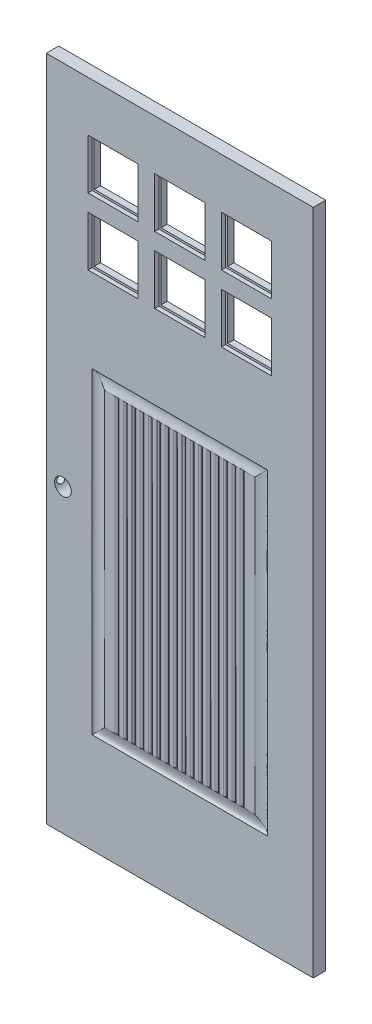
SolidWorks part; units mm, degrees
material "E-Glass Fiber"
ref_plane "Front Plane" through (0, 0, 0) normal (0, 0, 1) x (1, 0, 0)
ref_plane "Top Plane" through (0, 0, 0) normal (0, 1, 0) x (1, 0, 0)
ref_plane "Right Plane" through (0, 0, 0) normal (1, 0, 0) x (0, 0, -1)
sketch "Sketch1" plane through (0, 0, 0) normal (0, 0, 1) x (1, 0, 0)
  line L1 (-406.4, -1016) -> (406.4, -1016)
  line L2 (-406.4, -1016) -> (-406.4, 1016)
  line L3 (-406.4, 1016) -> (406.4, 1016)
  line L4 (406.4, -1016) -> (406.4, 1016)
  line L5 (-406.4, -1016) -> (406.4, 1016) construction
  line L6 (-406.4, 1016) -> (406.4, -1016) construction
  point P0 (0, 0)
  dimension "D1" = 2032
  dimension "D2" = 812.8
extrude "Boss-Extrude1" add sketch "Sketch1" along normal blind 38.1
sketch "Sketch2" plane through (0, 0, 38.1) normal (0, 0, 1) x (1, 0, 0)
  line L0 (406.4, 1016) -> (-406.4, 1016) construction
  line L1 (-279.4, 863.6) -> (-127, 863.6)
  line L2 (-279.4, 863.6) -> (-279.4, 711.2)
  line L3 (-279.4, 711.2) -> (-127, 711.2)
  line L4 (-127, 863.6) -> (-127, 711.2)
  line L5 (-279.4, 863.6) -> (-127, 711.2) construction
  line L6 (-279.4, 711.2) -> (-127, 863.6) construction
  line L7 (-406.4, 1016) -> (-406.4, -1016) construction
  line L8 (-76.2, 863.6) -> (-76.2, 711.2)
  line L9 (-76.2, 863.6) -> (76.2, 863.6)
  line L10 (76.2, 863.6) -> (76.2, 711.2)
  line L11 (-76.2, 711.2) -> (76.2, 711.2)
  line L12 (127, 863.6) -> (127, 711.2)
  line L13 (127, 863.6) -> (279.4, 863.6)
  line L14 (279.4, 863.6) -> (279.4, 711.2)
  line L15 (127, 711.2) -> (279.4, 711.2)
  line L16 (-76.2, 660.4) -> (-76.2, 508)
  line L17 (-76.2, 660.4) -> (76.2, 660.4)
  line L18 (76.2, 660.4) -> (76.2, 508)
  line L19 (-76.2, 508) -> (76.2, 508)
  line L20 (127, 660.4) -> (127, 508)
  line L21 (127, 660.4) -> (279.4, 660.4)
  line L22 (279.4, 660.4) -> (279.4, 508)
  line L23 (127, 508) -> (279.4, 508)
  line L24 (-279.4, 660.4) -> (-279.4, 508)
  line L25 (-279.4, 660.4) -> (-127, 660.4)
  line L26 (-127, 660.4) -> (-127, 508)
  line L27 (-279.4, 508) -> (-127, 508)
  line L30 (-406.4, -1016) -> (406.4, -1016) construction
  circle A0 centre (-355.6, -101.6) radius 25.4
  point P0 (-203.2, 787.4)
  dimension "D9" = 50.8
  dimension "D1" = 152.4
  dimension "D2" = 152.4
  dimension "D3" = 152.4
  dimension "D4" = 127
  dimension "D7" = 50.8
  dimension "D8" = 50.8
  dimension "D10" = 50.8
  dimension "D11" = 914.4
  dimension "D5" = 3
  dimension "D6" = 2
extrude "Cut-Extrude1" cut sketch "Sketch2" against normal up to surface (38.1 mm away) up to face at (0, 0, 0)
sketch "Sketch3" plane through (-406.4, 0, 0) normal (-1, 0, 0) x (0, 0, 1)
  line L1 (38.1, -1016) -> (0, -1016) construction
  circle A0 centre (19.05, -101.6) radius 12.7
  point P4 (19.05, -1016)
  dimension "D2" = 25.4
  dimension "D3" = 914.4
extrude "Cut-Extrude2" cut sketch "Sketch3" against normal up to surface (25.4 mm away)
sketch "Sketch4" plane through (0, 0, 38.1) normal (0, 0, 1) x (1, 0, 0)
  line L0 (-406.4, -1016) -> (406.4, -1016) construction
  line L1 (-266.7, 254) -> (266.7, 254)
  line L2 (-266.7, 254) -> (-266.7, -711.2)
  line L3 (-266.7, -711.2) -> (266.7, -711.2)
  line L4 (266.7, 254) -> (266.7, -711.2)
  line L5 (-266.7, 254) -> (266.7, -711.2) construction
  line L6 (-266.7, -711.2) -> (266.7, 254) construction
  line L7 (-76.2, 508) -> (76.2, 508) construction
  line L8 (-406.4, 1016) -> (-406.4, -1016) construction
  line L9 (406.4, -1016) -> (406.4, 1016) construction
  point P0 (0, -228.6)
  dimension "D1" = 304.8
  dimension "D2" = 254
  dimension "D3" = 139.7
  dimension "D4" = 139.7
sketch "Sketch5" plane through (0, 0, 0) normal (1, 0, 0) x (0, 0, -1)
  line L0 (-38.1, 254) -> (-38.1, 215.9)
  line L1 (-19.05, 1016) -> (-19.05, -1016) construction
  line L2 (-38.1, 1016) -> (0, 1016) construction
  line L3 (-38.1, -711.2) -> (-38.1, 254) construction
  line L4 (-38.1, -1016) -> (0, -1016) construction
  line L5 (0, 254) -> (0, 215.9)
  spline S0 degree 3 poles (-38.1, 215.9) (-37.7202, 218.0275) (-27.762, 241.9063) (-34.8576, 252.8292) (-38.1, 254) knots 0.037172 0.037172 0.037172 0.037172 0.768062 1 1 1 1
  spline S1 degree 3 poles (0, 215.9) (-0.3798, 218.0275) (-10.338, 241.9063) (-3.2424, 252.8292) (0, 254) knots 0.037172 0.037172 0.037172 0.037172 0.768062 1 1 1 1
  point P6 (0, 0)
  point P11 (0, 215.9)
  point P19 (0, 0)
  point P20 (0, 0)
  point P21 (0, 0)
  dimension "D1" = 38.1
sweep "Cut-Sweep1" cut profiles "Sketch5" path "Sketch4"
sketch "Sketch7" plane through (0, 0, 0) normal (0, 1, 0) x (1, 0, 0)
  line L2 (-184.15, -38.1) -> (-196.85, -38.1)
  line L3 (-228.6, -38.1) -> (228.6, -38.1) construction
  line L4 (406.4, -38.1) -> (-406.4, -38.1) construction
  line L5 (-406.4, -19.05) -> (406.4, -19.05) construction
  line L6 (-406.4, -38.1) -> (-406.4, 0) construction
  line L7 (406.4, -38.1) -> (406.4, 0) construction
  line L24 (-158.75, -38.1) -> (-171.45, -38.1)
  line L26 (-133.35, -38.1) -> (-146.05, -38.1)
  line L27 (-107.95, -38.1) -> (-120.65, -38.1)
  line L28 (-82.55, -38.1) -> (-95.25, -38.1)
  line L29 (-57.15, -38.1) -> (-69.85, -38.1)
  line L30 (-31.75, -38.1) -> (-44.45, -38.1)
  line L31 (-6.35, -38.1) -> (-19.05, -38.1)
  line L32 (19.05, -38.1) -> (6.35, -38.1)
  line L33 (44.45, -38.1) -> (31.75, -38.1)
  line L34 (69.85, -38.1) -> (57.15, -38.1)
  line L35 (95.25, -38.1) -> (82.55, -38.1)
  line L38 (120.65, -38.1) -> (107.95, -38.1)
  line L39 (146.05, -38.1) -> (133.35, -38.1)
  line L40 (171.45, -38.1) -> (158.75, -38.1)
  line L41 (196.85, -38.1) -> (184.15, -38.1)
  line L42 (196.85, 0) -> (184.15, 0)
  line L43 (171.45, 0) -> (158.75, 0)
  line L44 (146.05, 0) -> (133.35, 0)
  line L45 (120.65, 0) -> (107.95, 0)
  line L46 (95.25, 0) -> (82.55, 0)
  line L47 (69.85, 0) -> (57.15, 0)
  line L48 (44.45, 0) -> (31.75, 0)
  line L49 (19.05, 0) -> (6.35, 0)
  line L50 (-6.35, 0) -> (-19.05, 0)
  line L51 (-31.75, 0) -> (-44.45, 0)
  line L52 (-57.15, 0) -> (-69.85, 0)
  line L53 (-82.55, 0) -> (-95.25, 0)
  line L54 (-107.95, 0) -> (-120.65, 0)
  line L55 (-133.35, 0) -> (-146.05, 0)
  line L56 (-158.75, 0) -> (-171.45, 0)
  line L57 (-184.15, 0) -> (-196.85, 0)
  spline S0 degree 2 poles (-196.85, -38.1) (-191.5601, -37.3684) (-190.5, -31.75) knots 0 0 0 1 1 1
  spline S1 degree 2 poles (-184.15, -38.1) (-189.4399, -37.3684) (-190.5, -31.75) knots 0 0 0 1 1 1
  spline S2 degree 2 poles (-171.45, -38.1) (-166.1601, -37.3684) (-165.1, -31.75) knots 0 0 0 1 1 1
  spline S3 degree 2 poles (-158.75, -38.1) (-164.0399, -37.3684) (-165.1, -31.75) knots 0 0 0 1 1 1
  spline S4 degree 2 poles (82.55, -38.1) (87.8399, -37.3684) (88.9, -31.75) knots 0 0 0 1 1 1
  spline S5 degree 2 poles (95.25, -38.1) (89.9601, -37.3684) (88.9, -31.75) knots 0 0 0 1 1 1
  spline S6 degree 2 poles (-146.05, -38.1) (-140.7601, -37.3684) (-139.7, -31.75) knots 0 0 0 1 1 1
  spline S7 degree 2 poles (-133.35, -38.1) (-138.6399, -37.3684) (-139.7, -31.75) knots 0 0 0 1 1 1
  spline S8 degree 2 poles (-120.65, -38.1) (-115.3601, -37.3684) (-114.3, -31.75) knots 0 0 0 1 1 1
  spline S9 degree 2 poles (-107.95, -38.1) (-113.2399, -37.3684) (-114.3, -31.75) knots 0 0 0 1 1 1
  spline S10 degree 2 poles (-95.25, -38.1) (-89.9601, -37.3684) (-88.9, -31.75) knots 0 0 0 1 1 1
  spline S11 degree 2 poles (-82.55, -38.1) (-87.8399, -37.3684) (-88.9, -31.75) knots 0 0 0 1 1 1
  spline S12 degree 2 poles (-69.85, -38.1) (-64.5601, -37.3684) (-63.5, -31.75) knots 0 0 0 1 1 1
  spline S13 degree 2 poles (-57.15, -38.1) (-62.4399, -37.3684) (-63.5, -31.75) knots 0 0 0 1 1 1
  spline S14 degree 2 poles (-44.45, -38.1) (-39.1601, -37.3684) (-38.1, -31.75) knots 0 0 0 1 1 1
  spline S15 degree 2 poles (-31.75, -38.1) (-37.0399, -37.3684) (-38.1, -31.75) knots 0 0 0 1 1 1
  spline S16 degree 2 poles (-19.05, -38.1) (-13.7601, -37.3684) (-12.7, -31.75) knots 0 0 0 1 1 1
  spline S17 degree 2 poles (-6.35, -38.1) (-11.6399, -37.3684) (-12.7, -31.75) knots 0 0 0 1 1 1
  spline S18 degree 2 poles (6.35, -38.1) (11.6399, -37.3684) (12.7, -31.75) knots 0 0 0 1 1 1
  spline S19 degree 2 poles (19.05, -38.1) (13.7601, -37.3684) (12.7, -31.75) knots 0 0 0 1 1 1
  spline S20 degree 2 poles (31.75, -38.1) (37.0399, -37.3684) (38.1, -31.75) knots 0 0 0 1 1 1
  spline S21 degree 2 poles (44.45, -38.1) (39.1601, -37.3684) (38.1, -31.75) knots 0 0 0 1 1 1
  spline S22 degree 2 poles (57.15, -38.1) (62.4399, -37.3684) (63.5, -31.75) knots 0 0 0 1 1 1
  spline S23 degree 2 poles (69.85, -38.1) (64.5601, -37.3684) (63.5, -31.75) knots 0 0 0 1 1 1
  spline S24 degree 2 poles (133.35, -38.1) (138.6399, -37.3684) (139.7, -31.75) knots 0 0 0 1 1 1
  spline S25 degree 2 poles (146.05, -38.1) (140.7601, -37.3684) (139.7, -31.75) knots 0 0 0 1 1 1
  spline S26 degree 2 poles (158.75, -38.1) (164.0399, -37.3684) (165.1, -31.75) knots 0 0 0 1 1 1
  spline S27 degree 2 poles (171.45, -38.1) (166.1601, -37.3684) (165.1, -31.75) knots 0 0 0 1 1 1
  spline S28 degree 2 poles (107.95, -38.1) (113.2399, -37.3684) (114.3, -31.75) knots 0 0 0 1 1 1
  spline S29 degree 2 poles (120.65, -38.1) (115.3601, -37.3684) (114.3, -31.75) knots 0 0 0 1 1 1
  spline S30 degree 2 poles (184.15, -38.1) (189.4399, -37.3684) (190.5, -31.75) knots 0 0 0 1 1 1
  spline S31 degree 2 poles (196.85, -38.1) (191.5601, -37.3684) (190.5, -31.75) knots 0 0 0 1 1 1
  spline S32 degree 2 poles (196.85, 0) (191.5601, -0.7316) (190.5, -6.35) knots 0 0 0 1 1 1
  spline S33 degree 2 poles (184.15, 0) (189.4399, -0.7316) (190.5, -6.35) knots 0 0 0 1 1 1
  spline S34 degree 2 poles (120.65, 0) (115.3601, -0.7316) (114.3, -6.35) knots 0 0 0 1 1 1
  spline S35 degree 2 poles (107.95, 0) (113.2399, -0.7316) (114.3, -6.35) knots 0 0 0 1 1 1
  spline S36 degree 2 poles (171.45, 0) (166.1601, -0.7316) (165.1, -6.35) knots 0 0 0 1 1 1
  spline S37 degree 2 poles (158.75, 0) (164.0399, -0.7316) (165.1, -6.35) knots 0 0 0 1 1 1
  spline S38 degree 2 poles (146.05, 0) (140.7601, -0.7316) (139.7, -6.35) knots 0 0 0 1 1 1
  spline S39 degree 2 poles (133.35, 0) (138.6399, -0.7316) (139.7, -6.35) knots 0 0 0 1 1 1
  spline S40 degree 2 poles (69.85, 0) (64.5601, -0.7316) (63.5, -6.35) knots 0 0 0 1 1 1
  spline S41 degree 2 poles (57.15, 0) (62.4399, -0.7316) (63.5, -6.35) knots 0 0 0 1 1 1
  spline S42 degree 2 poles (44.45, 0) (39.1601, -0.7316) (38.1, -6.35) knots 0 0 0 1 1 1
  spline S43 degree 2 poles (31.75, 0) (37.0399, -0.7316) (38.1, -6.35) knots 0 0 0 1 1 1
  spline S44 degree 2 poles (19.05, 0) (13.7601, -0.7316) (12.7, -6.35) knots 0 0 0 1 1 1
  spline S45 degree 2 poles (6.35, 0) (11.6399, -0.7316) (12.7, -6.35) knots 0 0 0 1 1 1
  spline S46 degree 2 poles (-6.35, 0) (-11.6399, -0.7316) (-12.7, -6.35) knots 0 0 0 1 1 1
  spline S47 degree 2 poles (-19.05, 0) (-13.7601, -0.7316) (-12.7, -6.35) knots 0 0 0 1 1 1
  spline S48 degree 2 poles (-31.75, 0) (-37.0399, -0.7316) (-38.1, -6.35) knots 0 0 0 1 1 1
  spline S49 degree 2 poles (-44.45, 0) (-39.1601, -0.7316) (-38.1, -6.35) knots 0 0 0 1 1 1
  spline S50 degree 2 poles (-57.15, 0) (-62.4399, -0.7316) (-63.5, -6.35) knots 0 0 0 1 1 1
  spline S51 degree 2 poles (-69.85, 0) (-64.5601, -0.7316) (-63.5, -6.35) knots 0 0 0 1 1 1
  spline S52 degree 2 poles (-82.55, 0) (-87.8399, -0.7316) (-88.9, -6.35) knots 0 0 0 1 1 1
  spline S53 degree 2 poles (-95.25, 0) (-89.9601, -0.7316) (-88.9, -6.35) knots 0 0 0 1 1 1
  spline S54 degree 2 poles (-107.95, 0) (-113.2399, -0.7316) (-114.3, -6.35) knots 0 0 0 1 1 1
  spline S55 degree 2 poles (-120.65, 0) (-115.3601, -0.7316) (-114.3, -6.35) knots 0 0 0 1 1 1
  spline S56 degree 2 poles (-133.35, 0) (-138.6399, -0.7316) (-139.7, -6.35) knots 0 0 0 1 1 1
  spline S57 degree 2 poles (-146.05, 0) (-140.7601, -0.7316) (-139.7, -6.35) knots 0 0 0 1 1 1
  spline S58 degree 2 poles (95.25, 0) (89.9601, -0.7316) (88.9, -6.35) knots 0 0 0 1 1 1
  spline S59 degree 2 poles (82.55, 0) (87.8399, -0.7316) (88.9, -6.35) knots 0 0 0 1 1 1
  spline S60 degree 2 poles (-158.75, 0) (-164.0399, -0.7316) (-165.1, -6.35) knots 0 0 0 1 1 1
  spline S61 degree 2 poles (-171.45, 0) (-166.1601, -0.7316) (-165.1, -6.35) knots 0 0 0 1 1 1
  spline S62 degree 2 poles (-184.15, 0) (-189.4399, -0.7316) (-190.5, -6.35) knots 0 0 0 1 1 1
  spline S63 degree 2 poles (-196.85, 0) (-191.5601, -0.7316) (-190.5, -6.35) knots 0 0 0 1 1 1
  point P4 (-190.5, -38.1)
  point P21 (-165.1, -38.1)
  point P23 (0, 0)
  point P24 (-91.8618, -38.1)
  point P25 (-110.2838, -38.1)
  point P26 (-137.7567, -38.1)
  point P27 (-118.1332, -38.1)
  point P28 (-94.6651, -38.1)
  point P29 (-73.2796, -38.1)
  point P34 (-139.7, -38.1)
  point P40 (-114.3, -38.1)
  point P46 (-88.9, -38.1)
  point P52 (-63.5, -38.1)
  point P58 (-38.1, -38.1)
  point P64 (-12.7, -38.1)
  point P70 (12.7, -38.1)
  point P76 (38.1, -38.1)
  point P82 (63.5, -38.1)
  point P88 (88.9, -38.1)
  point P90 (184.8283, -38.1)
  point P91 (142.6746, -38.1)
  point P92 (124.5702, -38.1)
  point P93 (106.128, -38.1)
  point P94 (57.1514, -38.1)
  point P95 (43.7758, -38.1)
  point P96 (18.4431, -31.75)
  point P97 (0, 0)
  point P106 (114.3, -38.1)
  point P108 (27.8275, -38.1)
  point P109 (52.0894, -38.1)
  point P110 (-107.7102, -38.1)
  point P111 (-108.2757, -38.1)
  point P112 (-83.771, -38.1)
  point P113 (-48.2311, -38.1)
  point P114 (139.7, -38.1)
  point P116 (144.2744, -44.3619)
  point P121 (165.1, -38.1)
  point P123 (186.3202, -42.9563)
  point P128 (190.5, -38.1)
  point P130 (0, 0)
  dimension "D1" = 6.35
  dimension "D2" = 209.55
  dimension "D3" = 3.81
  dimension "D4" = 3.81
  dimension "D5" = 3.556
  dimension "D6" = 12.7
  dimension "D7" = 6.35
  dimension "D8" = 3.81
  dimension "D9" = 3.81
  dimension "D10" = 3.556
  dimension "D11" = 12.7
  dimension "D12" = 12.7
  dimension "D13" = 6.35
  dimension "D14" = 3.81
  dimension "D15" = 3.81
  dimension "D16" = 3.556
  dimension "D17" = 12.7
  dimension "D18" = 6.35
  dimension "D19" = 3.81
  dimension "D20" = 3.81
  dimension "D21" = 3.556
  dimension "D22" = 12.7
  dimension "D23" = 6.35
  dimension "D24" = 3.81
  dimension "D25" = 3.81
  dimension "D26" = 3.556
  dimension "D27" = 12.7
  dimension "D28" = 6.35
  dimension "D29" = 3.81
  dimension "D30" = 3.81
  dimension "D31" = 3.556
  dimension "D32" = 12.7
  dimension "D33" = 6.35
  dimension "D34" = 3.81
  dimension "D35" = 3.81
  dimension "D36" = 3.556
  dimension "D37" = 12.7
  dimension "D38" = 6.35
  dimension "D39" = 3.81
  dimension "D40" = 3.81
  dimension "D41" = 3.556
  dimension "D42" = 12.7
  dimension "D43" = 6.35
  dimension "D44" = 3.81
  dimension "D45" = 3.81
  dimension "D46" = 3.556
  dimension "D47" = 12.7
  dimension "D48" = 6.35
  dimension "D49" = 3.81
  dimension "D50" = 3.81
  dimension "D51" = 3.556
  dimension "D52" = 12.7
  dimension "D53" = 6.35
  dimension "D54" = 3.81
  dimension "D55" = 3.81
  dimension "D56" = 3.556
  dimension "D57" = 12.7
  dimension "D58" = 6.35
  dimension "D59" = 3.81
  dimension "D60" = 3.81
  dimension "D61" = 3.556
  dimension "D62" = 12.7
  dimension "D63" = 12.7
  dimension "D64" = 12.7
  dimension "D65" = 12.7
  dimension "D66" = 12.7
  dimension "D67" = 12.7
  dimension "D68" = 12.7
  dimension "D69" = 12.7
  dimension "D70" = 6.35
  dimension "D71" = 3.81
  dimension "D72" = 3.81
  dimension "D73" = 6.35
  dimension "D74" = 3.81
  dimension "D75" = 3.81
  dimension "D76" = 3.556
  dimension "D77" = 12.7
  dimension "D78" = 12.7
  dimension "D79" = 12.7
  dimension "D80" = 12.7
  dimension "D81" = 12.7
  dimension "D82" = 3.556
  dimension "D83" = 12.7
  dimension "D84" = 6.35
  dimension "D85" = 3.81
  dimension "D86" = 3.81
  dimension "D87" = 3.556
  dimension "D88" = 12.7
  dimension "D89" = 12.7
  dimension "D90" = 12.7
  dimension "D91" = 6.35
  dimension "D92" = 3.81
  dimension "D93" = 3.81
  dimension "D94" = 3.556
  dimension "D95" = 12.7
  dimension "D96" = 12.7
sketch "Sketch8" plane through (-406.4, 0, 0) normal (-1, 0, 0) x (0, 0, 1)
  line L0 (19.05, 215.9) -> (19.05, -673.1)
  line L3 (38.1, 1016) -> (0, 1016) construction
  line L4 (38.1, -1016) -> (0, -1016) construction
  point P11 (19.05, 1016)
  point P13 (19.05, -1016)
  dimension "D1" = 800.1
  dimension "D2" = 342.9
sweep "Cut-Sweep4" cut profiles "Sketch7" path "Sketch8"
sketch "Sketch9" plane through (0, 508, 0) normal (0, 1, 0) x (1, 0, 0)
  line L0 (-279.4, 0) -> (-279.4, -38.1) construction
  line L1 (-285.75, -19.05) -> (285.75, -19.05)
  line L2 (-285.75, -19.05) -> (-285.75, -25.4)
  line L3 (-285.75, -25.4) -> (285.75, -25.4)
  line L4 (285.75, -19.05) -> (285.75, -25.4)
  line L5 (-285.75, -19.05) -> (285.75, -25.4) construction
  line L6 (-285.75, -25.4) -> (285.75, -19.05) construction
  line L7 (279.4, 0) -> (279.4, -38.1) construction
  line L8 (76.2, 0) -> (76.2, -38.1) construction
  point P0 (0, -22.225)
  point P5 (0, 0)
  point P8 (285.75, -22.225)
  point P11 (0, -16.6865)
  point P14 (76.2, -19.05)
  dimension "D1" = 6.35
  dimension "D2" = 6.35
  dimension "D3" = 6.35
extrude "Cut-Extrude3" cut sketch "Sketch9" along normal offset from surface 6.35 and the other way blind 6.35 up to face at (-203.2, 863.6, 19.05) offset beyond the face yes
